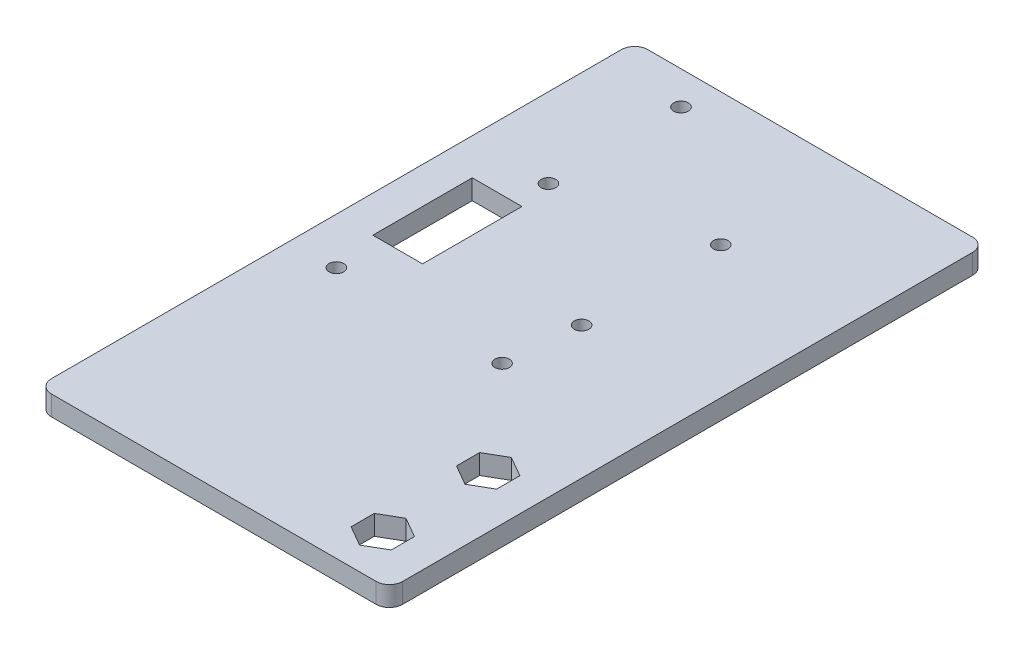
SolidWorks part; units mm, degrees
ref_plane "Plan de face" through (0, 0, 0) normal (0, 0, 1) x (1, 0, 0)
ref_plane "Plan de dessus" through (0, 0, 0) normal (0, 1, 0) x (1, 0, 0)
ref_plane "Plan de droite" through (0, 0, 0) normal (1, 0, 0) x (0, 0, -1)
sketch "Esquisse1" plane through (0, 0, 0) normal (0, 1, 0) x (1, 0, 0)
  line L6 (0, 88) -> (0, 2)
  line L7 (2, 0) -> (51, 0)
  line L8 (53, 88) -> (53, 2)
  line L11 (2, 90) -> (51, 90)
  arc A0 (51, 90) -> (53, 88) centre (51, 88) cw
  arc A1 (2, 90) -> (0, 88) centre (2, 88) ccw
  arc A2 (51, 0) -> (53, 2) centre (51, 2) ccw
  arc A3 (0, 2) -> (2, 0) centre (2, 2) ccw
  point P3 (26.5, 0)
  dimension "D3" = 2
  dimension "D5" = 2
  dimension "D4" = 2
  dimension "D1" = 53
  dimension "D2" = 90
extrude "Extrusion1" add sketch "Esquisse1" along normal blind 3
sketch "Esquisse4" plane through (0, 3, 0) normal (0, 1, 0) x (1, 0, 0)
  line L0 (51, 90) -> (2, 90) construction
  line L1 (0, 88) -> (0, 2) construction
  line L3 (5.5, 60) -> (13, 60)
  line L4 (5.5, 60) -> (5.5, 45)
  line L5 (5.5, 45) -> (13, 45)
  line L6 (13, 60) -> (13, 45)
  circle A0 centre (12, 85) radius 1.1
  circle A1 centre (12, 65) radius 1.1
  dimension "D1" = 2.2
  dimension "D2" = 5
  dimension "D4" = 12
  dimension "D3" = 20
  dimension "D5" = 15
  dimension "D6" = 7.5
  dimension "D7" = 5
  dimension "D8" = 1
extrude "Enlèv. mat.-Extru.2" cut sketch "Esquisse4" against normal through all
sketch "Esquisse2" plane through (0, 0, 0) normal (0, -1, 0) x (1, 0, 0)
  line L0 (53, -2) -> (53, -88) construction
  line L2 (2, 0) -> (51, 0) construction
  circle A12 centre (45, -22.9029) radius 1.1
  circle A13 centre (45, -7) radius 1.1
  dimension "D35" = 2.2
  dimension "D36" = 2.2
  dimension "D32" = 15.9029
  dimension "D33" = 8
  dimension "D34" = 7
extrude "Enlèv. mat.-Extru.1" cut sketch "Esquisse2" against normal through all
sketch "Esquisse6" plane through (0, 3, 0) normal (0, 1, 0) x (1, 0, 0)
  line L0 (53, 2) -> (53, 88) construction
  line L1 (41.9689, 8.75) -> (41.9689, 5.25)
  line L2 (41.9689, 5.25) -> (45, 3.5)
  line L3 (45, 3.5) -> (48.0311, 5.25)
  line L4 (48.0311, 5.25) -> (48.0311, 8.75)
  line L5 (48.0311, 8.75) -> (45, 10.5)
  line L6 (45, 10.5) -> (41.9689, 8.75)
  line L7 (41.9689, 24.6529) -> (41.9689, 21.1529)
  line L8 (41.9689, 21.1529) -> (45, 19.4029)
  line L9 (45, 19.4029) -> (48.0311, 21.1529)
  line L10 (48.0311, 21.1529) -> (48.0311, 24.6529)
  line L11 (48.0311, 24.6529) -> (45, 26.4029)
  line L12 (45, 26.4029) -> (41.9689, 24.6529)
  line L13 (51, 90) -> (2, 90) construction
  circle A0 centre (45, 7) radius 3.0311 construction
  circle A1 centre (45, 22.9029) radius 3.0311 construction
  circle A2 centre (45, 7) radius 1.1 construction
  circle A3 centre (45, 22.9029) radius 1.1 construction
  circle A4 centre (33, 70) radius 1.1
  circle A5 centre (33, 49) radius 1.1
  dimension "D6" = 2.2
  dimension "D1" = 3.5
  dimension "D2" = 3.5
  dimension "D3" = 20
  dimension "D4" = 21
  dimension "D5" = 20
extrude "Enlèv. mat.-Extru.3" cut sketch "Esquisse6" against normal through all
sketch "Esquisse7" plane through (0, 3, 0) normal (0, 1, 0) x (1, 0, 0)
  line L0 (0, 88) -> (0, 2) construction
  line L1 (5.5, 45) -> (13, 45) construction
  line L2 (51, 90) -> (2, 90) construction
  circle A0 centre (7, 38) radius 1.1
  circle A1 centre (32, 38) radius 1.1
  dimension "D2" = 2.2
  dimension "D1" = 25
  dimension "D3" = 7
  dimension "D4" = 7
  dimension "D5" = 52
extrude "Enlèv. mat.-Extru.4" cut sketch "Esquisse7" against normal through all
